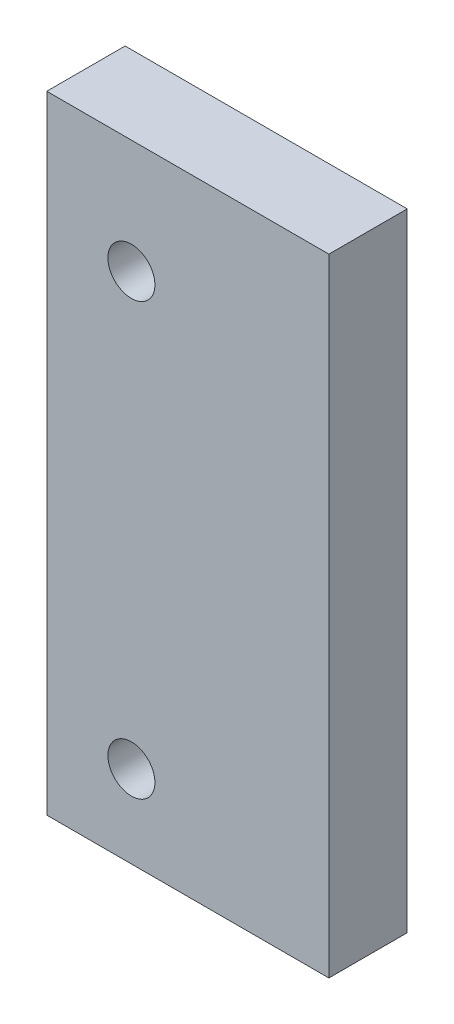
SolidWorks part; units mm, degrees
ref_plane "Front Plane" through (0, 0, 0) normal (0, 0, 1) x (1, 0, 0)
ref_plane "Top Plane" through (0, 0, 0) normal (0, 1, 0) x (1, 0, 0)
ref_plane "Right Plane" through (0, 0, 0) normal (1, 0, 0) x (0, 0, -1)
sketch "Sketch2" plane through (0, 0, 0) normal (0, 0, 1) x (1, 0, 0)
  line L0 (0, 0) -> (0, 20)
  line L1 (0, 20) -> (9, 20)
  line L2 (9, 20) -> (9, 0)
  line L3 (9, 0) -> (0, 0)
  dimension "D1" = 9
  dimension "D2" = 20
extrude "Boss-Extrude1" add sketch "Sketch2" along normal blind 2.5
sketch "Sketch3" plane through (0, 0, 2.5) normal (0, 0, 1) x (1, 0, 0)
  line L0 (0, 20) -> (0, 0) construction
  line L1 (9, 20) -> (0, 20) construction
  line L2 (0, 0) -> (9, 0) construction
  circle A0 centre (2.7, 16.375) radius 0.75
  circle A1 centre (2.7, 2.625) radius 0.75
  dimension "D1" = 2.7
  dimension "D2" = 2.7
  dimension "D3" = 3.625
  dimension "D4" = 2.625
  dimension "D5" = 1.5
  dimension "D6" = 1.5
extrude "Cut-Extrude1" cut sketch "Sketch3" against normal through all
